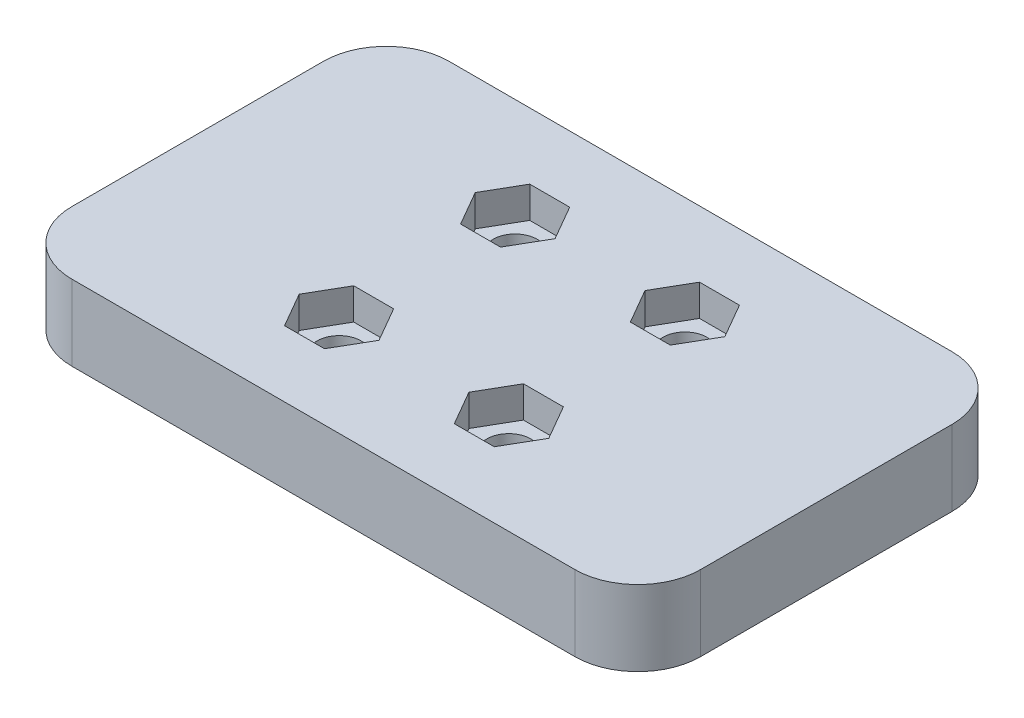
SolidWorks part; units mm, degrees
ref_plane "Front Plane" through (0, 0, 0) normal (0, 0, 1) x (1, 0, 0)
ref_plane "Top Plane" through (0, 0, 0) normal (0, 1, 0) x (1, 0, 0)
ref_plane "Right Plane" through (0, 0, 0) normal (1, 0, 0) x (0, 0, -1)
sketch "Sketch1" plane through (0, 0, 0) normal (0, 1, 0) x (1, 0, 0)
  line L0 (18.25, 7) -> (31.75, 7) construction
  line L1 (5, 0) -> (45, 0)
  line L2 (0, 5) -> (0, 10)
  line L3 (5, 15) -> (45, 15)
  line L4 (50, 5) -> (50, 10)
  circle A0 centre (18.25, 7) radius 1.75
  circle A1 centre (31.75, 7) radius 1.75
  arc A2 (0, 5) -> (5, 0) centre (5, 5) ccw
  arc A3 (50, 5) -> (45, 0) centre (45, 5) cw
  arc A4 (45, 15) -> (50, 10) centre (45, 10) cw
  arc A5 (0, 10) -> (5, 15) centre (5, 10) cw
  point P10 (25, 7)
  point P11 (25, 0)
  point P14 (0, 0)
  point P17 (50, 0)
  point P22 (0, 15)
  dimension "D3" = 3.5
  dimension "D6" = 5
  dimension "D1" = 50
  dimension "D2" = 15
  dimension "D4" = 13.5
  dimension "D5" = 7
extrude "Boss-Extrude1" add sketch "Sketch1" along normal blind 6
sketch "Sketch2" plane through (0, 6, 0) normal (0, 1, 0) x (1, 0, 0)
  line L1 (19.8377, 4.25) -> (21.4254, 7)
  line L2 (21.4254, 7) -> (19.8377, 9.75)
  line L3 (19.8377, 9.75) -> (16.6623, 9.75)
  line L4 (16.6623, 9.75) -> (15.0746, 7)
  line L5 (15.0746, 7) -> (16.6623, 4.25)
  line L6 (16.6623, 4.25) -> (19.8377, 4.25)
  line L7 (33.3377, 4.25) -> (34.9254, 7)
  line L8 (34.9254, 7) -> (33.3377, 9.75)
  line L9 (33.3377, 9.75) -> (30.1623, 9.75)
  line L10 (30.1623, 9.75) -> (28.5746, 7)
  line L11 (28.5746, 7) -> (30.1623, 4.25)
  line L12 (30.1623, 4.25) -> (33.3377, 4.25)
  line L13 (5, 0) -> (45, 0) construction
  circle A0 centre (18.25, 7) radius 2.75 construction
  circle A1 centre (31.75, 7) radius 2.75 construction
  dimension "D1" = 5.5
extrude "Cut-Extrude1" cut sketch "Sketch2" against normal blind 2.5
mirror "Mirror1" about plane through (0, 0, 0) normal (0, 0, 1) of "Cut-Extrude1", "Boss-Extrude1"
sketch "Sketch3" plane through (0, 6, 0) normal (0, 1, 0) x (1, 0, 0)
  line L0 (50, 5) -> (50, -5)
  line L1 (0, 5) -> (0, -5)
  arc A0 (50, -5) -> (45, 0) centre (45, -5) ccw construction
  arc A1 (45, 0) -> (50, 5) centre (45, 5) ccw construction
  arc A2 (0, 5) -> (5, 0) centre (5, 5) ccw construction
  arc A3 (5, 0) -> (0, -5) centre (5, -5) ccw construction
  arc A4 (50, -5) -> (45, 0) centre (45, -5) ccw
  arc A5 (45, 0) -> (50, 5) centre (45, 5) ccw
  arc A6 (0, 5) -> (5, 0) centre (5, 5) ccw
  arc A7 (5, 0) -> (0, -5) centre (5, -5) ccw
extrude "Boss-Extrude2" add sketch "Sketch3" against normal up to surface (6 mm away) up to face at (25, 0, 0)
